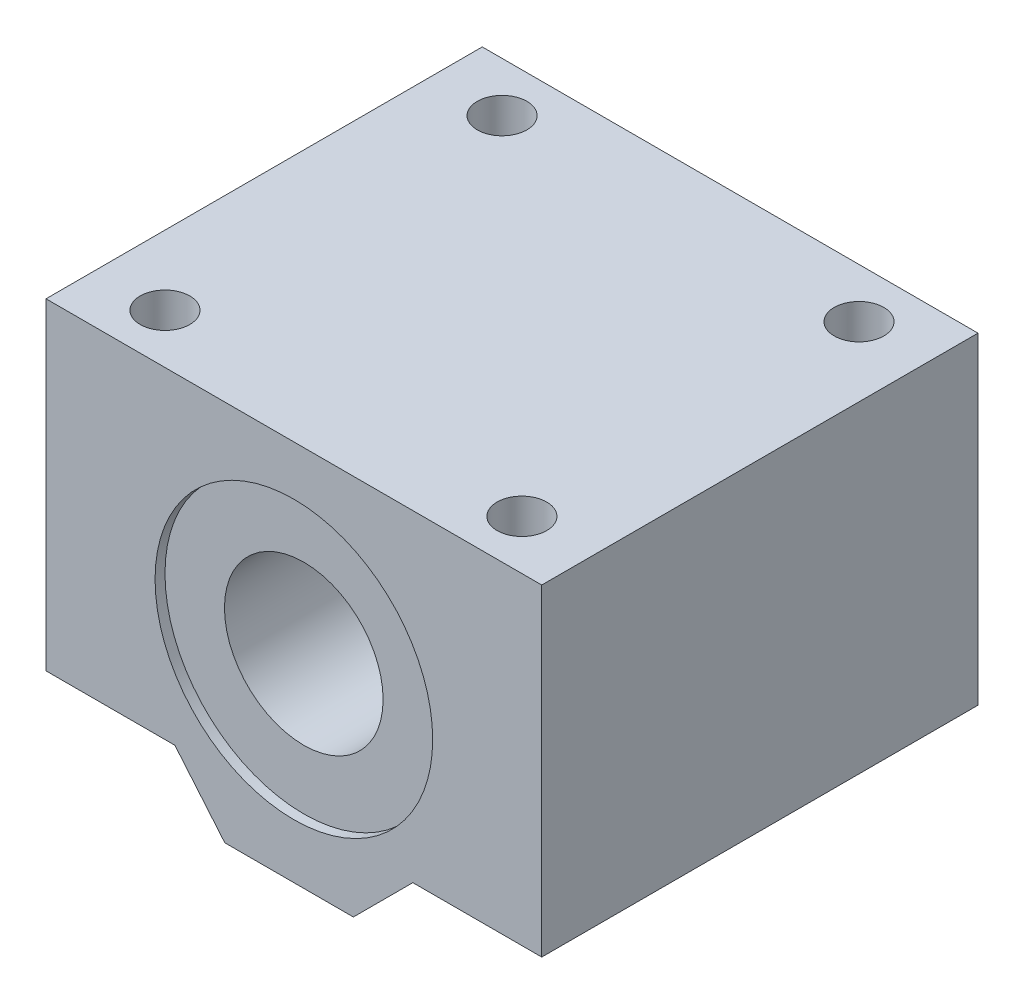
SolidWorks part; units mm, degrees
ref_plane "Front Plane" through (0, 0, 0) normal (0, 0, 1) x (1, 0, 0)
ref_plane "Top Plane" through (0, 0, 0) normal (0, 1, 0) x (1, 0, 0)
ref_plane "Right Plane" through (0, 0, 0) normal (1, 0, 0) x (0, 0, -1)
sketch "Sketch1" plane through (0, 0, 0) normal (0, 0, 1) x (1, 0, 0)
  line L1 (-25, -19.25) -> (25, -19.25)
  line L2 (-25, -19.25) -> (-25, 19.25)
  line L3 (-25, 19.25) -> (25, 19.25)
  line L4 (25, -19.25) -> (25, 19.25)
  line L5 (-25, -19.25) -> (25, 19.25) construction
  line L6 (-25, 19.25) -> (25, -19.25) construction
  circle A0 centre (0, 0.25) radius 8
  point P0 (0, 0)
  dimension "D3" = 16
  dimension "D1" = 50
  dimension "D2" = 38.5
  dimension "D4" = 25
  dimension "D5" = 19
extrude "Boss-Extrude1" add sketch "Sketch1" along normal mid plane 44
sketch "Sketch6" plane through (0, 0, 22) normal (0, 0, 1) x (1, 0, 0)
  line L1 (-25, 19.25) -> (-25, -19.25) construction
  line L7 (25, -19.25) -> (25, 19.25) construction
  line L11 (-25, -13.25) -> (-12, -13.25)
  line L12 (-12, -13.25) -> (-6.9654, -19.25)
  line L13 (-25, -19.25) -> (25, -19.25) construction
  line L14 (-6.9654, -19.25) -> (-25, -19.25)
  line L15 (-25, -19.25) -> (-25, -13.25)
  line L16 (25, -13.25) -> (12, -13.25)
  line L17 (12, -13.25) -> (6, -19.25)
  line L18 (6, -19.25) -> (25, -19.25)
  line L19 (25, -19.25) -> (25, -13.25)
  dimension "D6" = 13
  dimension "D7" = 135
  dimension "D8" = 6
  dimension "D9" = 130
  dimension "D10" = 13
extrude "Cut-Extrude5" cut sketch "Sketch6" against normal through all
sketch "Sketch2" plane through (0, 19.25, 0) normal (0, -1, 0) x (-1, 0, 0)
  line L0 (0, -18) -> (0, 18) construction
  line L3 (21, 0) -> (-21, 0) construction
  circle A0 centre (18, -17) radius 2.15
  circle A1 centre (-18, -17) radius 2.15
  circle A2 centre (-18, 17) radius 2.15
  circle A3 centre (18, 17) radius 2.15
  dimension "D1" = 4.3
  dimension "D2" = 4.3
  dimension "D3" = 4.3
  dimension "D4" = 4.3
  dimension "D5" = 18
  dimension "D6" = 18
  dimension "D7" = 18
  dimension "D8" = 18
  dimension "D9" = 17
  dimension "D10" = 17
  dimension "D11" = 17
  dimension "D12" = 17
extrude "Cut-Extrude1" cut sketch "Sketch2" along normal through all
sketch "Sketch3" plane through (0, 19.25, 0) normal (0, -1, 0) x (1, 0, 0)
  circle A0 centre (-18, 17) radius 2.5
  circle A1 centre (18, 17) radius 2.5
  circle A2 centre (18, -17) radius 2.5
  circle A3 centre (-18, -17) radius 2.5
  dimension "D1" = 5
  dimension "D2" = 5
  dimension "D3" = 5
  dimension "D4" = 5
extrude "Cut-Extrude2" cut sketch "Sketch3" along normal blind 12
sketch "Sketch4" plane through (0, 0, 22) normal (0, 0, 1) x (1, 0, 0)
  circle A0 centre (0, 0.25) radius 14
  dimension "D1" = 28
extrude "Cut-Extrude3" cut sketch "Sketch4" against normal blind 1
sketch "Sketch5" plane through (0, 0, -22) normal (0, 0, -1) x (-1, 0, 0)
  circle A0 centre (0, 0.25) radius 14
  dimension "D1" = 28
extrude "Cut-Extrude4" cut sketch "Sketch5" against normal blind 1
equation "\"D10@Sketch6\"=\"D6@Sketch6\""
equation "\"D5@Sketch2\"=36/2"
equation "\"D6@Sketch2\"=\"D5@Sketch2\""
equation "\"D8@Sketch2\"=\"D5@Sketch2\""
equation "\"D7@Sketch2\"=\"D5@Sketch2\""
equation "\"D10@Sketch2\"=34/2"
equation "\"D9@Sketch2\"=\"D10@Sketch2\""
equation "\"D12@Sketch2\"=\"D9@Sketch2\""
equation "\"D11@Sketch2\"=\"D10@Sketch2\""
